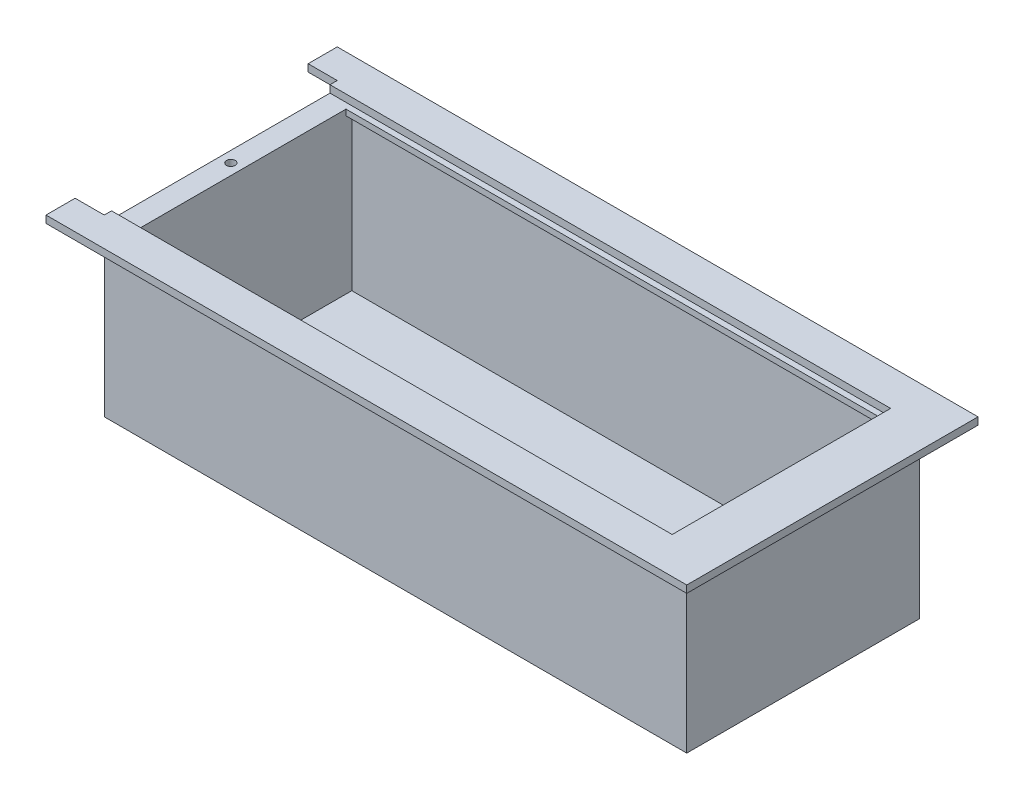
SolidWorks part; units mm, degrees
ref_plane "Front Plane" through (0, 0, 0) normal (0, 0, 1) x (1, 0, 0)
ref_plane "Top Plane" through (0, 0, 0) normal (0, 1, 0) x (1, 0, 0)
ref_plane "Right Plane" through (0, 0, 0) normal (1, 0, 0) x (0, 0, -1)
sketch "Sketch1" plane through (0, 0, 0) normal (0, 0, 1) x (1, 0, 0)
  line L1 (0, 0) -> (200, 0)
  line L2 (0, 0) -> (0, 60)
  line L3 (0, 60) -> (200, 60)
  line L4 (200, 0) -> (200, 60)
  dimension "D1" = 200
  dimension "D2" = 60
extrude "Boss-Extrude1" add sketch "Sketch1" along normal blind 80
sketch "Sketch2" plane through (0, 60, 0) normal (0, 1, 0) x (1, 0, 0)
  line L0 (100, -80) -> (100, 0) construction
  line L1 (200, -80) -> (0, -80) construction
  line L2 (200, 0) -> (0, 0) construction
  line L3 (200, -40) -> (0, -40) construction
  line L4 (200, -80) -> (200, 0) construction
  line L5 (0, -80) -> (0, 0) construction
  line L7 (192.5, -77.5) -> (7.5, -77.5)
  line L8 (192.5, -77.5) -> (192.5, -2.5)
  line L9 (192.5, -2.5) -> (7.5, -2.5)
  line L10 (7.5, -77.5) -> (7.5, -2.5)
  dimension "D1" = 185
  dimension "D2" = 75
  dimension "D3" = 2.5
  dimension "D4" = 7.5
extrude "Cut-Extrude1" cut sketch "Sketch2" against normal blind 57.5
sketch "Sketch3" plane through (0, 60, 0) normal (0, 1, 0) x (1, 0, 0)
  line L0 (0, -80) -> (0, 0) construction
  line L1 (7.5, -77.5) -> (0, -77.5)
  line L2 (7.5, -77.5) -> (7.5, -2.5)
  line L3 (7.5, -2.5) -> (0, -2.5)
  line L4 (0, -77.5) -> (0, -2.5)
  dimension "D1" = 75
  dimension "D2" = 7.5
extrude "Cut-Extrude2" cut sketch "Sketch3" against normal blind 2.5
sketch "Sketch4" plane through (0, 0, 0) normal (0, 0, -1) x (-1, 0, 0)
  line L0 (-200, 0) -> (-200, 60) construction
  line L1 (-200, 60) -> (10, 60)
  line L2 (-200, 60) -> (-200, 57.5)
  line L3 (-200, 57.5) -> (10, 57.5)
  line L4 (10, 60) -> (10, 57.5)
  line L5 (-200, 60) -> (0, 60) construction
  dimension "D1" = 210
  dimension "D2" = 0
  dimension "D3" = 0
  dimension "D4" = 2.5
extrude "Boss-Extrude7" add sketch "Sketch4" along normal blind 10
sketch "Sketch9" plane through (0, 0, 80) normal (0, 0, 1) x (1, 0, 0)
  line L0 (200, 60) -> (0, 60) construction
  line L1 (-10, 60) -> (200, 60)
  line L2 (-10, 60) -> (-10, 57.5)
  line L3 (-10, 57.5) -> (200, 57.5)
  line L4 (200, 60) -> (200, 57.5)
  line L5 (200, 0) -> (200, 60) construction
  dimension "D1" = 0
  dimension "D2" = 0
  dimension "D3" = 2.5
  dimension "D4" = 210
extrude "Boss-Extrude8" add sketch "Sketch9" along normal blind 10
sketch "Sketch10" plane through (200, 0, 0) normal (1, 0, 0) x (0, 0, -1)
  line L0 (-90, 60) -> (10, 60) construction
  line L1 (-90, 60) -> (10, 60)
  line L2 (-90, 60) -> (-90, 57.5)
  line L3 (-90, 57.5) -> (10, 57.5)
  line L4 (10, 60) -> (10, 57.5)
  line L5 (10, 60) -> (10, 57.5) construction
  dimension "D1" = 0
  dimension "D2" = 2.5
  dimension "D3" = 0
  dimension "D4" = 100
extrude "Boss-Extrude9" add sketch "Sketch10" along normal blind 10
sketch "Sketch11" plane through (0, 57.5, 0) normal (0, 1, 0) x (1, 0, 0)
  line L0 (3.75, -77.5) -> (3.75, -3.0306) construction
  line L1 (0, -77.5) -> (7.5, -77.5) construction
  line L2 (0, -40) -> (7.5, -40) construction
  line L3 (0, -2.5) -> (0, -77.5) construction
  line L4 (7.5, -77.5) -> (7.5, -2.5) construction
  circle A0 centre (3.75, -40.2653) radius 1.5
  dimension "D1" = 3
extrude "Cut-Extrude3" cut sketch "Sketch11" against normal blind 5
sketch "Sketch12" plane through (0, 0, 77.5) normal (0, 0, -1) x (-1, 0, 0)
  line L0 (-192.5, 2.5) -> (-192.5, 60) construction
  line L1 (-7.5, 57.5) -> (-192.5, 57.5)
  line L2 (-7.5, 57.5) -> (-7.5, 55.5)
  line L3 (-7.5, 55.5) -> (-192.5, 55.5)
  line L4 (-192.5, 57.5) -> (-192.5, 55.5)
  point P5 (-192.5, 56.5)
  dimension "D1" = 0
  dimension "D2" = 185
  dimension "D3" = 2
extrude "Boss-Extrude11" add sketch "Sketch12" along normal blind 2
sketch "Sketch13" plane through (0, 0, 2.5) normal (0, 0, 1) x (1, 0, 0)
  line L0 (7.5, 2.5) -> (7.5, 57.5) construction
  line L1 (7.5, 57.5) -> (192.5, 57.5)
  line L2 (7.5, 57.5) -> (7.5, 55.5)
  line L3 (7.5, 55.5) -> (192.5, 55.5)
  line L4 (192.5, 57.5) -> (192.5, 55.5)
  line L5 (192.5, 2.5) -> (192.5, 60) construction
  line L6 (192.5, 60) -> (0, 60) construction
  dimension "D1" = 2
  dimension "D2" = 2.5
extrude "Boss-Extrude12" add sketch "Sketch13" along normal blind 2
sketch "Sketch14" plane through (192.5, 0, 0) normal (-1, 0, 0) x (0, 0, 1)
  line L0 (77.5, 60) -> (2.5, 60) construction
  line L1 (12.5, 57.5) -> (67.5, 57.5)
  line L2 (12.5, 57.5) -> (12.5, 55)
  line L3 (12.5, 55) -> (67.5, 55)
  line L4 (67.5, 57.5) -> (67.5, 55)
  line L7 (2.5, 57.5) -> (2.5, 60) construction
  line L8 (77.5, 2.5) -> (77.5, 55.5) construction
  dimension "D1" = 2.5
  dimension "D2" = 10
  dimension "D3" = 2.5
  dimension "D4" = 10
extrude "Cut-Extrude4" cut sketch "Sketch14" against normal blind 3
sketch "Sketch15" plane through (0, 2.5, 0) normal (0, 1, 0) x (1, 0, 0)
  line L0 (7.5, -77.5) -> (192.5, -77.5) construction
  line L1 (42.5, -47.5) -> (17.5, -47.5)
  line L2 (42.5, -47.5) -> (42.5, -32.5)
  line L3 (42.5, -32.5) -> (17.5, -32.5)
  line L4 (17.5, -47.5) -> (17.5, -32.5)
  line L6 (192.5, -2.5) -> (7.5, -2.5) construction
  line L7 (7.5, -2.5) -> (7.5, -77.5) construction
  dimension "D1" = 30
  dimension "D2" = 30
  dimension "D3" = 15
  dimension "D4" = 25
  dimension "D5" = 10
extrude "Cut-Extrude5" cut sketch "Sketch15" against normal up to surface (2.5 mm away) up to face at (100, 0, 40)
